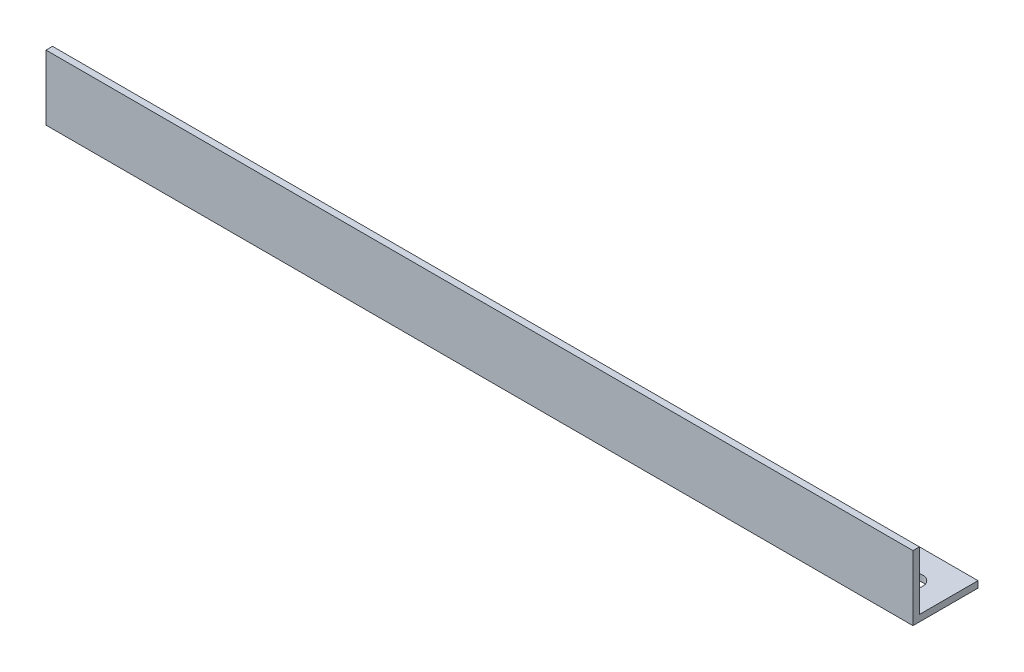
SolidWorks part; units mm, degrees
ref_plane "Спереди" through (0, 0, 0) normal (0, 0, 1) x (1, 0, 0)
ref_plane "Сверху" through (0, 0, 0) normal (0, 1, 0) x (1, 0, 0)
ref_plane "Справа" through (0, 0, 0) normal (1, 0, 0) x (0, 0, -1)
sketch "Эскиз1" plane through (0, 0, 0) normal (1, 0, 0) x (0, 0, -1)
  line L0 (0, 0) -> (0, 15)
  line L1 (0, 15) -> (1.5, 15)
  line L2 (1.5, 15) -> (1.5, 1.5)
  line L3 (1.5, 1.5) -> (15, 1.5)
  line L4 (15, 1.5) -> (15, 0)
  line L5 (15, 0) -> (0, 0)
  dimension "D1" = 15
  dimension "D2" = 15
  dimension "D3" = 1.5
  dimension "D4" = 1.5
extrude "Бобышка-Вытянуть1" add sketch "Эскиз1" along normal blind 200
sketch "Эскиз2" plane through (0, 0, 0) normal (0, -1, 0) x (1, 0, 0)
  line L0 (0, 0) -> (0, -15) construction
  line L1 (200, 0) -> (200, -15) construction
  circle A0 centre (7.5, -7.5) radius 2.25
  circle A1 centre (192.5, -7.5) radius 2.25
  dimension "D1" = 4.5
  dimension "D2" = 7.5
  dimension "D3" = 4.5
  dimension "D4" = 7.5
extrude "Вырез-Вытянуть1" cut sketch "Эскиз2" against normal through all
